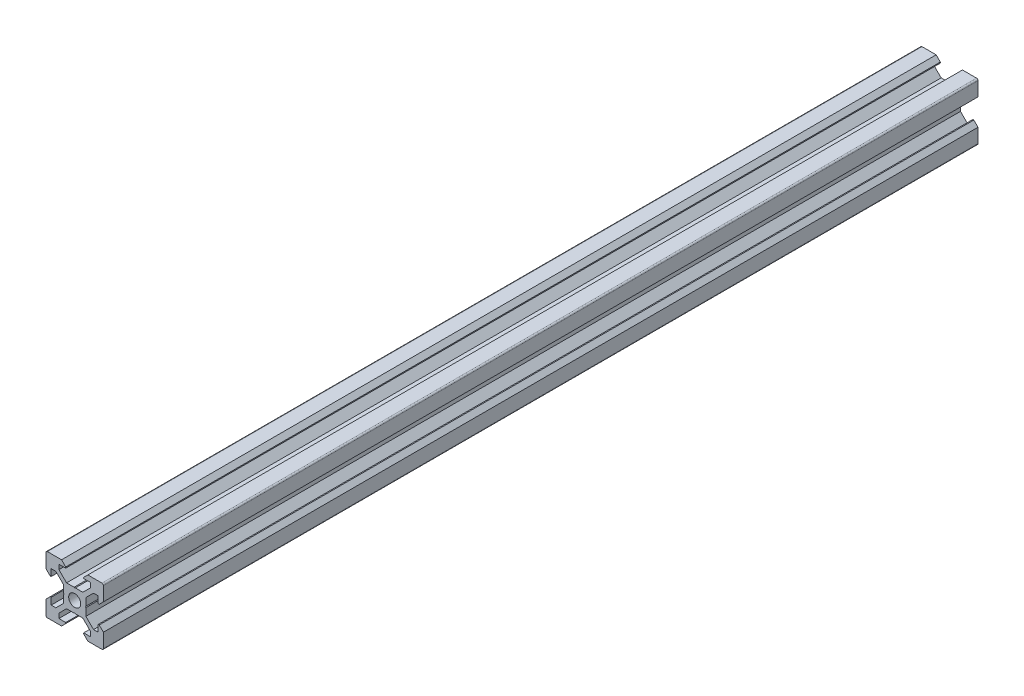
SolidWorks part; units mm, degrees
material "6061-T6 (SS)"
ref_plane "Front Plane" through (0, 0, 0) normal (0, 0, 1) x (1, 0, 0)
ref_plane "Top Plane" through (0, 0, 0) normal (0, 1, 0) x (1, 0, 0)
ref_plane "Right Plane" through (0, 0, 0) normal (1, 0, 0) x (0, 0, -1)
ref_plane "Plane1" through (0, 0, 0) normal (0, 0, -1) x (-1, 0, 0)
sketch "Sketch1" plane through (0, 0, 0) normal (0, 0, -1) x (-1, 0, 0)
  line L0 (-3.9, -0.21) -> (-3.9, -2.8393)
  line L1 (-3.9, -2.8393) -> (-6.5607, -5.5)
  line L2 (-6.5607, -5.5) -> (-8.2, -5.5)
  line L3 (-8.2, -5.5) -> (-8.2, -3.125)
  line L4 (-8.2, -3.125) -> (-8.545, -3.125)
  line L5 (-8.545, -3.125) -> (-10, -4.58)
  line L6 (-10, -4.58) -> (-10, -9.5)
  line L7 (-9.5, -10) -> (-4.58, -10)
  line L8 (-4.58, -10) -> (-3.125, -8.545)
  line L9 (-3.125, -8.545) -> (-3.125, -8.2)
  line L10 (-3.125, -8.2) -> (-5.5, -8.2)
  line L11 (-5.5, -8.2) -> (-5.5, -6.5607)
  line L12 (-5.5, -6.5607) -> (-2.8393, -3.9)
  line L13 (-2.8393, -3.9) -> (-0.21, -3.9)
  line L14 (-0.21, -3.9) -> (0, -3.69)
  line L15 (0, -3.69) -> (0.21, -3.9)
  line L16 (0.21, -3.9) -> (2.8393, -3.9)
  line L17 (2.8393, -3.9) -> (5.5, -6.5607)
  line L18 (5.5, -6.5607) -> (5.5, -8.2)
  line L19 (5.5, -8.2) -> (3.125, -8.2)
  line L20 (3.125, -8.2) -> (3.125, -8.545)
  line L21 (3.125, -8.545) -> (4.58, -10)
  line L22 (4.58, -10) -> (9.5, -10)
  line L23 (10, -9.5) -> (10, -4.58)
  line L24 (10, -4.58) -> (8.545, -3.125)
  line L25 (8.545, -3.125) -> (8.2, -3.125)
  line L26 (8.2, -3.125) -> (8.2, -5.5)
  line L27 (8.2, -5.5) -> (6.5607, -5.5)
  line L28 (6.5607, -5.5) -> (3.9, -2.8393)
  line L29 (3.9, -2.8393) -> (3.9, -0.21)
  line L30 (3.9, -0.21) -> (3.69, 0)
  line L31 (3.69, 0) -> (3.9, 0.21)
  line L32 (3.9, 0.21) -> (3.9, 2.8393)
  line L33 (3.9, 2.8393) -> (6.5607, 5.5)
  line L34 (6.5607, 5.5) -> (8.2, 5.5)
  line L35 (8.2, 5.5) -> (8.2, 3.125)
  line L36 (8.2, 3.125) -> (8.545, 3.125)
  line L37 (8.545, 3.125) -> (10, 4.58)
  line L38 (10, 4.58) -> (10, 9.5)
  line L39 (9.5, 10) -> (4.58, 10)
  line L40 (4.58, 10) -> (3.125, 8.545)
  line L41 (3.125, 8.545) -> (3.125, 8.2)
  line L42 (3.125, 8.2) -> (5.5, 8.2)
  line L43 (5.5, 8.2) -> (5.5, 6.5607)
  line L44 (5.5, 6.5607) -> (2.8393, 3.9)
  line L45 (2.8393, 3.9) -> (0.21, 3.9)
  line L46 (0.21, 3.9) -> (0, 3.69)
  line L47 (0, 3.69) -> (-0.21, 3.9)
  line L48 (-0.21, 3.9) -> (-2.8393, 3.9)
  line L49 (-2.8393, 3.9) -> (-5.5, 6.5607)
  line L50 (-5.5, 6.5607) -> (-5.5, 8.2)
  line L51 (-5.5, 8.2) -> (-3.125, 8.2)
  line L52 (-3.125, 8.2) -> (-3.125, 8.545)
  line L53 (-3.125, 8.545) -> (-4.58, 10)
  line L54 (-4.58, 10) -> (-9.5, 10)
  line L55 (-10, 9.5) -> (-10, 4.58)
  line L56 (-10, 4.58) -> (-8.545, 3.125)
  line L57 (-8.545, 3.125) -> (-8.2, 3.125)
  line L58 (-8.2, 3.125) -> (-8.2, 5.5)
  line L59 (-8.2, 5.5) -> (-6.5607, 5.5)
  line L60 (-6.5607, 5.5) -> (-3.9, 2.8393)
  line L61 (-3.9, 2.8393) -> (-3.9, 0.21)
  line L62 (-3.9, 0.21) -> (-3.69, 0)
  line L63 (-3.69, 0) -> (-3.9, -0.21)
  circle A0 centre (0, 0) radius 2.1
  arc A1 (-10, -9.5) -> (-9.5, -10) centre (-9.5, -9.5) ccw
  arc A2 (9.5, -10) -> (10, -9.5) centre (9.5, -9.5) ccw
  arc A3 (10, 9.5) -> (9.5, 10) centre (9.5, 9.5) ccw
  arc A4 (-9.5, 10) -> (-10, 9.5) centre (-9.5, 9.5) ccw
extrude "Boss-Extrude1" add sketch "Sketch1" against normal blind 500
cosmetic thread "Cosmetic Thread1" parameters "D1"=12.7, "D2"=5
ref_plane "cut plane" through (0, 0, 195.2) normal (0, 0, 1) x (1, 0, 0)
split "Split1" trim tools "cut plane" bodies to split 103 resulting bodies 105
